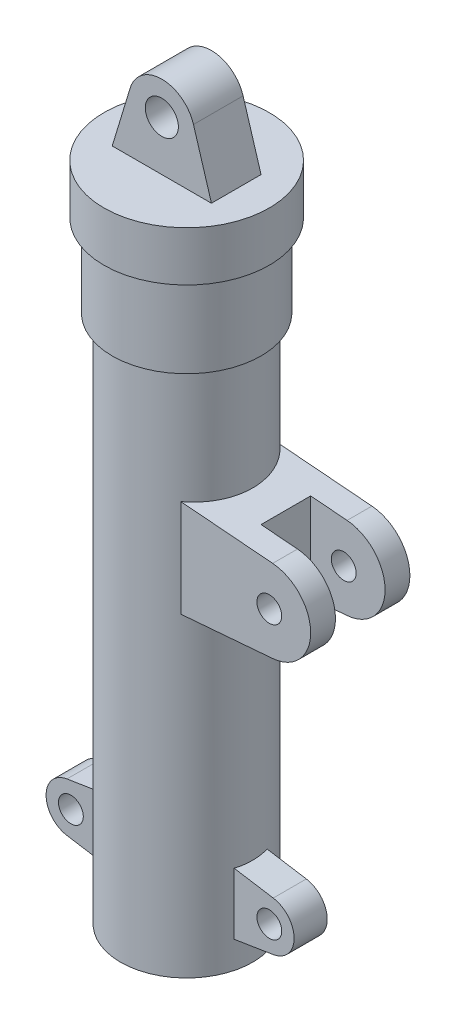
SolidWorks part; units mm, degrees
ref_plane "Plane1" through (0, 0, 0) normal (0, 0, 1) x (1, 0, 0)
ref_plane "Plane2" through (0, 0, 0) normal (0, 1, 0) x (1, 0, 0)
ref_plane "Plane3" through (0, 0, 0) normal (1, 0, 0) x (0, 0, -1)
other "Configuration Table"
sketch "Sketch1" plane through (0, 0, 0) normal (0, 0, 1) x (1, 0, 0)
  line L0 (22.5, -330) -> (40, -330)
  line L1 (0, 55) -> (0, 70)
  line L2 (50, 70) -> (0, 70)
  line L3 (40, -10) -> (40, -330)
  line L4 (45, -10) -> (45, 40)
  line L5 (50, 40) -> (50, 70)
  line L6 (50, 40) -> (45, 40)
  line L7 (45, -10) -> (40, -10)
  line L8 (22.5, -330) -> (22.5, -325)
  line L9 (22.5, -325) -> (35, -325)
  line L10 (35, -325) -> (35, 55)
  line L11 (35, 55) -> (0, 55)
  line L12 (0, 100) -> (0, -90) construction
  dimension "D1" = 400
  dimension "D2" = 50
  dimension "D3" = 40
  dimension "D4" = 35
  dimension "D5" = 22.5
  dimension "D6" = 5
  dimension "D7" = 15
  dimension "D8" = 30
  dimension "D9" = 5
  dimension "D10" = 80
revolve "Base-Revolve" add sketch "Sketch1" angle 360 about L12
sketch "Sketch2" plane through (0, 0, 0) normal (0, 0, 1) x (1, 0, 0)
  line L0 (19.1389, 105.8055) -> (30, 70)
  line L1 (50, 70) -> (-50, 70) construction
  line L2 (-19.1389, 105.8055) -> (-30, 70)
  line L3 (0, 100) -> (0, -90) construction
  line L4 (30, 70) -> (-30, 70)
  arc A0 (19.1389, 105.8055) -> (-19.1389, 105.8055) centre (0, 100) ccw
  circle A1 centre (0, 100) radius 10
  dimension "D2" = 20
  dimension "D3" = 20
  dimension "D1" = 60
  dimension "D5" = 30
extrude "Boss-Extrude1" add sketch "Sketch2" along normal mid plane 30
sketch "Sketch3" plane through (0, 0, 0) normal (0, 0, 1) x (1, 0, 0)
  line L0 (62.374, -280.189) -> (30, -275)
  line L1 (30, -275) -> (30, -315)
  line L3 (30, -315) -> (62.374, -309.811)
  line L4 (40, -330) -> (-40, -330) construction
  arc A0 (62.374, -280.189) -> (62.374, -309.811) centre (60, -295) cw
  circle A1 centre (60, -295) radius 7.5
  dimension "D2" = 15
  dimension "D4" = 15
  dimension "D1" = 40
  dimension "D3" = 30
  dimension "D5" = 35
  dimension "D6" = 30
extrude "Boss-Extrude2" add sketch "Sketch3" along normal mid plane 20
mirror "Mirror1" about plane through (0, 0, 0) normal (1, 0, 0) of "Boss-Extrude2"
sketch "Sketch8" plane through (0, 0, 0) normal (0, 0, 1) x (1, 0, 0)
  line L0 (82.0416, -85.0835) -> (20, -80)
  line L1 (20, -80) -> (20, -140)
  line L2 (45, -10) -> (-45, -10) construction
  line L3 (20, -140) -> (82.0416, -134.9165)
  arc A0 (82.0416, -85.0835) -> (82.0416, -134.9165) centre (80, -110) cw
  circle A1 centre (80, -110) radius 7.5
  dimension "D2" = 25
  dimension "D4" = 15
  dimension "D1" = 60
  dimension "D3" = 60
  dimension "D5" = 100
  dimension "D6" = 20
extrude "Boss-Extrude3" add sketch "Sketch8" along normal mid plane 60
sketch "Sketch4" plane through (0, 0, 0) normal (0, 0, 1) x (1, 0, 0)
  line L0 (0, -10) -> (35, -10)
  line L1 (0, -10) -> (0, -325)
  line L2 (35, -325) -> (0, -325)
  line L3 (35, -325) -> (35, -10)
  line L5 (35, -325) -> (-35, -325) construction
  line L6 (45, -10) -> (-45, -10) construction
  line L7 (0, 0) -> (0, -130) construction
  dimension "D1" = 35
revolve "Cut-Revolve1" cut sketch "Sketch4" angle 360 about L7
sketch "Sketch9" plane through (0, 0, 0) normal (0, 0, 1) x (1, 0, 0)
  line L0 (60, -70) -> (130, -70)
  line L1 (60, -70) -> (60, -150)
  line L2 (130, -150) -> (60, -150)
  line L3 (130, -150) -> (130, -70)
  arc A0 (82.0416, -134.9165) -> (82.0416, -85.0835) centre (80, -110) ccw construction
  dimension "D1" = 80
  dimension "D2" = 70
  dimension "D3" = 20
  dimension "D4" = 40
extrude "Cut-Extrude1" cut sketch "Sketch9" against normal mid plane 30
